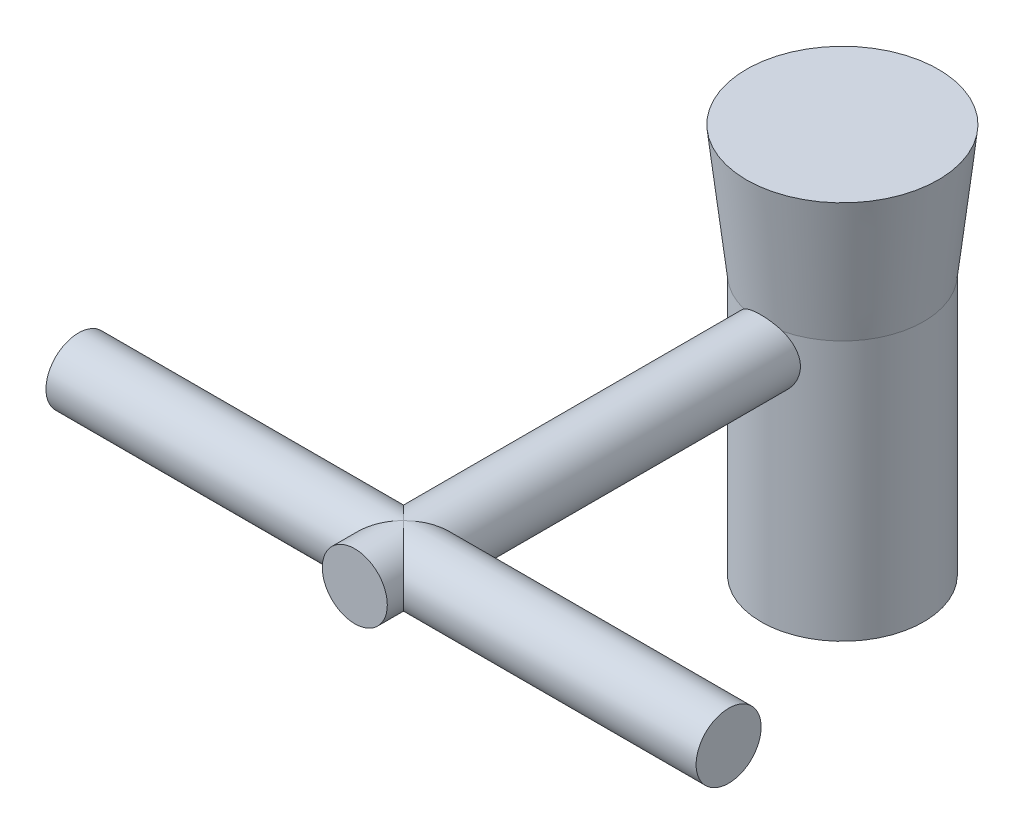
SolidWorks part; units mm, degrees
ref_plane "Front Plane" through (0, 0, 0) normal (0, 0, 1) x (1, 0, 0)
ref_plane "Top Plane" through (0, 0, 0) normal (0, 1, 0) x (1, 0, 0)
ref_plane "Right Plane" through (0, 0, 0) normal (1, 0, 0) x (0, 0, -1)
sketch "Sketch1" plane through (0, 0, 0) normal (0, 1, 0) x (1, 0, 0)
  circle A0 centre (0, 0) radius 12.5
  dimension "D1" = 25
extrude "Boss-Extrude1" add sketch "Sketch1" along normal blind 40
sketch "Sketch2" plane through (0, 40, 0) normal (0, 1, 0) x (1, 0, 0)
  circle A1 centre (0, 0) radius 12.5
  circle A2 centre (0, 0) radius 12.5
  dimension "D1" = 0
ref_plane "Plane1" through (0, 60, 0) normal (0, 1, 0) x (1, 0, 0)
sketch "Sketch3" plane through (0, 60, 0) normal (0, 1, 0) x (1, 0, 0)
  circle A0 centre (0, 0) radius 14.75
  dimension "D1" = 29.5
loft "Loft1" add profiles "Sketch3", "Sketch2"
sketch "Sketch4" plane through (0, 0, 0) normal (0, 0, 1) x (1, 0, 0)
  line L0 (0, 36) -> (0, 60) construction
  line L1 (14.75, 60) -> (-14.75, 60) construction
  circle A0 centre (0, 36) radius 5
  dimension "D1" = 24
  dimension "D2" = 10
extrude "Boss-Extrude2" add sketch "Sketch4" along normal blind 75
ref_plane "Plane3" through (0, 0, 12.5) normal (0, 0, 1) x (1, 0, 0)
sketch "Sketch5" plane through (0, 0, 0) normal (1, 0, 0) x (0, 0, -1)
  line L0 (-67.5, 36) -> (-12.5, 36) construction
  line L1 (-12.5, 36) -> (-12.5, 41) construction
  line L2 (-12.6125, 41) -> (-75, 41) construction
  line L3 (-12.5, 36) -> (-12.5, 31) construction
  line L4 (-75, 31) -> (-12.5, 31) construction
  line L5 (-12.5, 31) -> (-12.5, 0) construction
  line L6 (-62.5, 36) -> (-62.5, 48.2883) construction
  circle A0 centre (-67.5, 36) radius 5
  dimension "D1" = 10
  dimension "D3" = 50
extrude "Boss-Extrude3" add sketch "Sketch5" along normal mid plane 100
